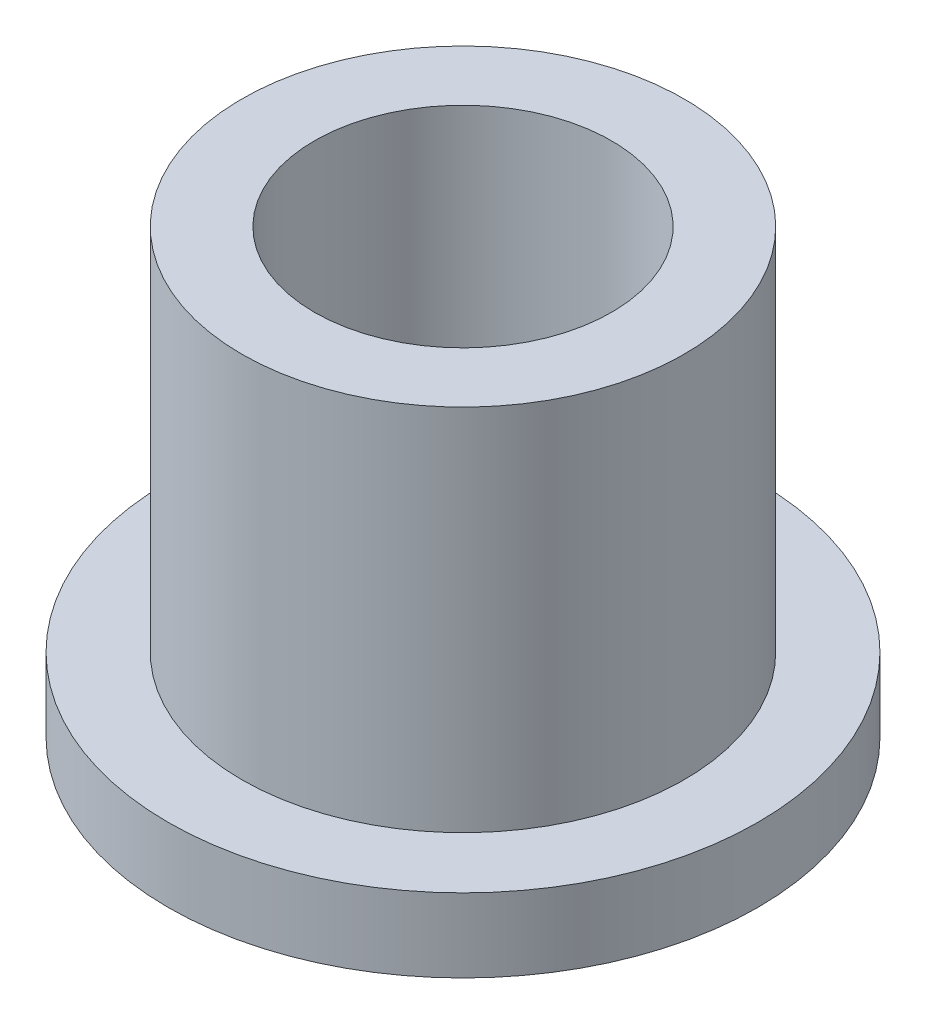
SolidWorks part; units mm, degrees
material "Rulon LR"
ref_plane "Front" through (0, 0, 0) normal (0, 0, 1) x (1, 0, 0)
ref_plane "Top" through (0, 0, 0) normal (0, 1, 0) x (1, 0, 0)
ref_plane "Right" through (0, 0, 0) normal (1, 0, 0) x (0, 0, -1)
sketch "Sketch1" plane through (0, 0, 0) normal (0, 1, 0) x (1, 0, 0)
  circle A0 centre (0, 0) radius 6.4008
  circle A1 centre (0, 0) radius 9.525
  circle A2 centre (0, 0) radius 12.7
  dimension "ID" = 12.8016
  dimension "OD" = 19.05
  dimension "FlangeOD" = 25.4
sketch "Sketch2" plane through (0, 0, 0) normal (0, 1, 0) x (1, 0, 0)
  circle A0 centre (0, 0) radius 6.4008 construction
  circle A1 centre (0, 0) radius 9.525 construction
  circle A2 centre (0, 0) radius 6.4008
  circle A3 centre (0, 0) radius 9.525
extrude "Boss-Extrude1" add sketch "Sketch2" along normal blind 19.05
sketch "Sketch3" plane through (0, 0, 0) normal (0, 1, 0) x (1, 0, 0)
  circle A0 centre (0, 0) radius 12.7 construction
  circle A1 centre (0, 0) radius 9.525 construction
  circle A2 centre (0, 0) radius 12.7
  circle A3 centre (0, 0) radius 9.525
extrude "Boss-Extrude2" add sketch "Sketch3" along normal blind 3.175
